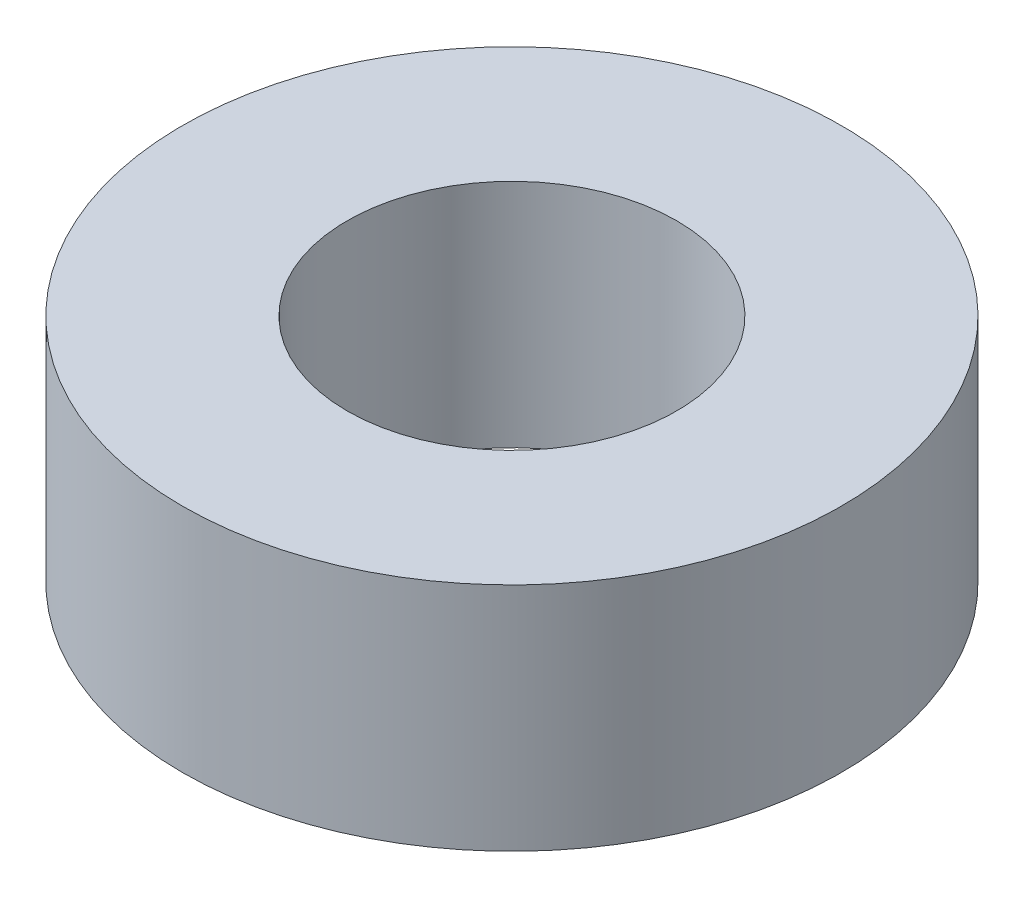
SolidWorks part; units mm, degrees
ref_plane "Front Plane" through (0, 0, 0) normal (0, 0, 1) x (1, 0, 0)
ref_plane "Top Plane" through (0, 0, 0) normal (0, 1, 0) x (1, 0, 0)
ref_plane "Right Plane" through (0, 0, 0) normal (1, 0, 0) x (0, 0, -1)
sketch "Sketch1" plane through (0, 0, 0) normal (0, 1, 0) x (1, 0, 0)
  circle A0 centre (0, 0) radius 40
  circle A1 centre (0, 0) radius 20
  dimension "D1" = 80
  dimension "D2" = 40
extrude "Boss-Extrude1" add sketch "Sketch1" along normal blind 28
